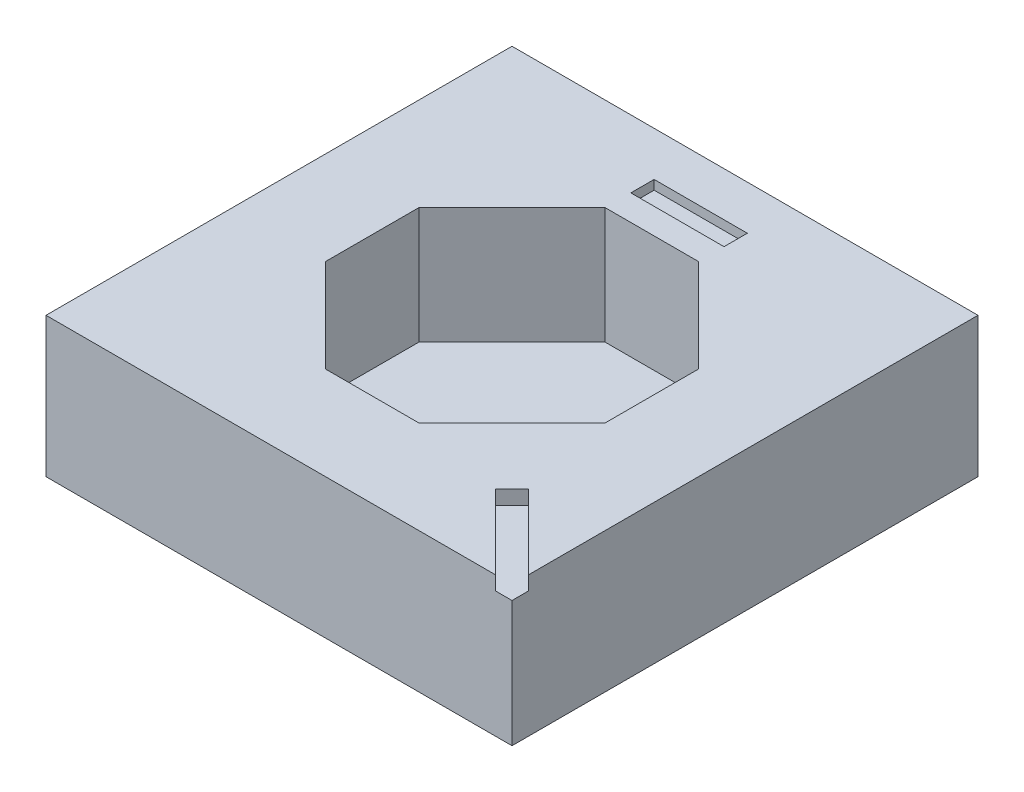
SolidWorks part; units mm, degrees
ref_plane "Front Plane" through (0, 0, 0) normal (0, 0, 1) x (1, 0, 0)
ref_plane "Top Plane" through (0, 0, 0) normal (0, 1, 0) x (1, 0, 0)
ref_plane "Right Plane" through (0, 0, 0) normal (1, 0, 0) x (0, 0, -1)
sketch "Sketch1" plane through (0, 0, 0) normal (0, 1, 0) x (1, 0, 0)
  line L1 (50, 50) -> (-50, 50)
  line L2 (50, 50) -> (50, -50)
  line L3 (50, -50) -> (-50, -50)
  line L4 (-50, 50) -> (-50, -50)
  line L5 (50, 50) -> (-50, -50) construction
  line L6 (50, -50) -> (-50, 50) construction
  point P0 (0, 0)
  dimension "D1" = 100
extrude "Boss-Extrude1" add sketch "Sketch1" along normal blind 30 contours L4 L3 L2 L1
sketch "Sketch2" plane through (0, 30, 0) normal (0, 1, 0) x (1, 0, 0)
  line L0 (30, 10) -> (10, 30)
  line L1 (-10, 30) -> (-30, 10)
  line L2 (-30, -10) -> (-10, -30)
  line L3 (10, -30) -> (30, -10)
  line L8 (30, 30) -> (-30, 30)
  line L9 (-30, 30) -> (-30, -30)
  line L10 (-30, -30) -> (30, -30)
  line L11 (30, -30) -> (30, 30)
  line L12 (10, 30) -> (-10, 30)
  line L13 (-30, 10) -> (-30, -10)
  line L14 (-10, -30) -> (10, -30)
  line L15 (30, -10) -> (30, 10)
  dimension "D2" = 60
  dimension "D1" = 20
extrude "Cut-Extrude1" cut sketch "Sketch2" against normal offset from surface (25 mm away) 5 up to face at (0, 0, 0)
sketch "Sketch3" plane through (0, 30, 0) normal (0, 1, 0) x (1, 0, 0)
  line L0 (-10, 38) -> (10, 38)
  line L2 (0, 38) -> (0, 50) construction
  line L3 (50, 50) -> (-50, 50) construction
  dimension "D1" = 12
  dimension "D2" = 20
extrude "Cut-Extrude-Thin1" cut sketch "Sketch3" against normal blind 2 thin contours L0 thin type mid plane wall 5
sketch "Sketch4" plane through (0, 30, 0) normal (0, 1, 0) x (1, 0, 0)
  line L0 (50, -50) -> (32.3223, -32.3223)
  line L1 (50, -50) -> (-50, -50) construction
  point P3 (28.5782, -35.6081)
  dimension "D1" = 45
  dimension "D2" = 25
extrude "Cut-Extrude-Thin2" cut sketch "Sketch4" against normal blind 3 and the other way through all thin thin type mid plane wall 5
